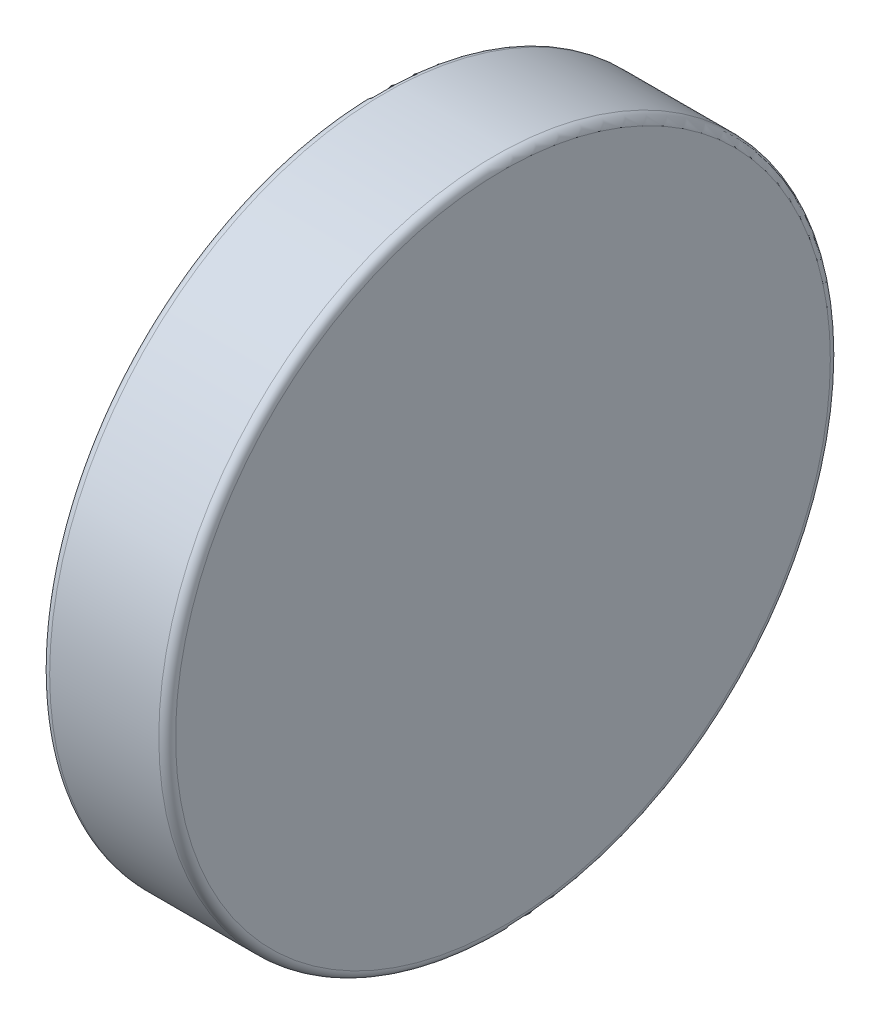
SolidWorks part; units mm, degrees
ref_plane "Front Plane" through (0, 0, 0) normal (1, 0, 0) x (0, 1, 0)
ref_plane "Top Plane" through (0, 0, 0) normal (0, 0, 1) x (0, 1, 0)
ref_plane "Right Plane" through (0, 0, 0) normal (0, 1, 0) x (-1, 0, 0)
sketch "Sketch1" plane through (0, 0, 0) normal (1, 0, 0) x (0, 1, 0)
  circle A0 centre (0, 0) radius 4
  dimension "D1" = 8
extrude "Boss-Extrude1" add sketch "Sketch1" along normal blind 1.5
fillet "Fillet1" radius 0.1 2 edges at (1.5, 0, -4) (0, 0, -4)
